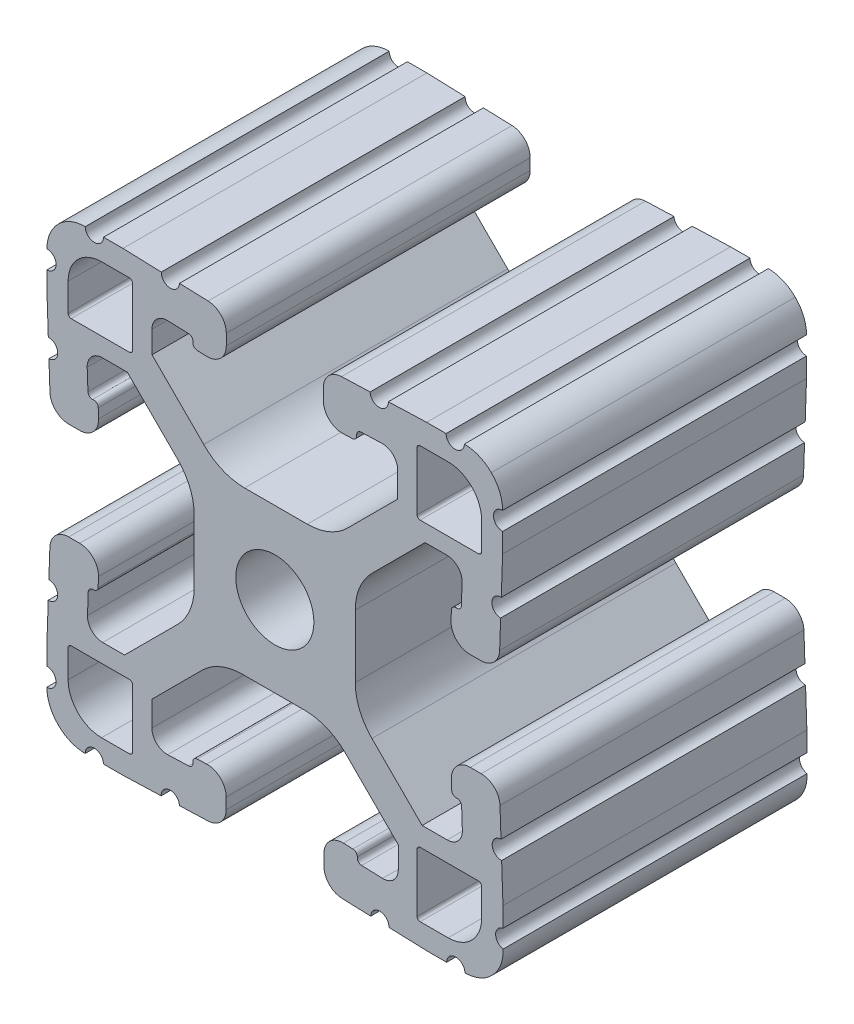
SolidWorks part; units mm, degrees
ref_plane "Front Plane" through (0, 0, 0) normal (0, 0, 1) x (1, 0, 0)
ref_plane "Top Plane" through (0, 0, 0) normal (0, 1, 0) x (1, 0, 0)
ref_plane "Right Plane" through (0, 0, 0) normal (1, 0, 0) x (0, 0, -1)
ref_plane "Plane1" through (0, 0, -25.4) normal (0, 0, -1) x (-1, 0, 0)
sketch "Sketch1" plane through (0, 0, -25.4) normal (0, 0, -1) x (-1, 0, 0)
  line L0 (-83.3577, 88.2941) -> (-83.3577, 93.1709)
  line L1 (-83.1037, 93.4249) -> (-80.767, 93.4249)
  line L2 (-77.9729, 90.6309) -> (-77.9729, 88.2941)
  line L3 (-78.2269, 88.0401) -> (-83.1037, 88.0401)
  line L4 (-83.3577, 59.2291) -> (-83.3577, 64.1059)
  line L5 (-83.1037, 64.3599) -> (-78.2269, 64.3599)
  line L6 (-77.9729, 64.1059) -> (-77.9729, 61.7691)
  line L7 (-80.767, 58.9751) -> (-83.1037, 58.9751)
  line L8 (-107.1423, 93.1709) -> (-107.1423, 88.2941)
  line L9 (-107.3963, 88.0401) -> (-112.2731, 88.0401)
  line L10 (-112.5271, 88.2941) -> (-112.5271, 90.6309)
  line L11 (-109.733, 93.4249) -> (-107.3963, 93.4249)
  line L12 (-107.1423, 64.1059) -> (-107.1423, 59.2291)
  line L13 (-107.3963, 58.9751) -> (-109.733, 58.9751)
  line L14 (-112.5271, 61.7691) -> (-112.5271, 64.1059)
  line L15 (-112.2731, 64.3599) -> (-107.3963, 64.3599)
  line L16 (-88.0437, 91.8626) -> (-86.2967, 91.9236)
  line L17 (-84.9824, 90.6544) -> (-84.9824, 88.8002)
  line L18 (-84.9824, 88.8002) -> (-89.3066, 84.476)
  line L19 (-92.7196, 83.0295) -> (-97.9616, 83.0295)
  line L20 (-101.3202, 84.4207) -> (-105.516, 88.6165)
  line L21 (-105.516, 88.6165) -> (-105.516, 90.7313)
  line L22 (-104.2017, 92.0006) -> (-102.4547, 91.9396)
  line L23 (-101.7262, 91.1059) -> (-100.9297, 91.0781)
  line L24 (-99.2999, 92.6519) -> (-99.2999, 93.5668)
  line L25 (-100.8197, 95.1407) -> (-103.2119, 95.2242)
  line L26 (-104.735, 95.2774) -> (-107.9359, 95.3892)
  line L27 (-107.9359, 95.3892) -> (-109.5615, 95.3892)
  line L28 (-114.2859, 90.6648) -> (-114.2859, 89.0392)
  line L29 (-114.2859, 89.0392) -> (-114.1741, 85.8383)
  line L30 (-114.1209, 84.3152) -> (-114.0374, 81.9231)
  line L31 (-112.4635, 80.4032) -> (-111.5486, 80.4032)
  line L32 (-109.9748, 82.033) -> (-110.0026, 82.8295)
  line L33 (-110.8377, 83.5577) -> (-110.8987, 85.3047)
  line L34 (-109.6294, 86.619) -> (-107.8072, 86.619)
  line L35 (-107.8072, 86.619) -> (-103.3649, 82.1768)
  line L36 (-101.9737, 78.8182) -> (-101.9737, 73.576)
  line L37 (-103.3649, 70.2174) -> (-107.5607, 66.0217)
  line L38 (-107.5607, 66.0217) -> (-109.6524, 66.0217)
  line L39 (-110.9217, 67.336) -> (-110.8607, 69.083)
  line L40 (-110.0322, 69.8124) -> (-110.0043, 70.6089)
  line L41 (-111.5782, 72.2387) -> (-112.4931, 72.2387)
  line L42 (-114.0669, 70.7189) -> (-114.1505, 68.3267)
  line L43 (-114.2036, 66.8036) -> (-114.3154, 63.6027)
  line L44 (-114.3154, 63.6027) -> (-114.3154, 61.9626)
  line L45 (-109.6111, 57.1437) -> (-107.9855, 57.1437)
  line L46 (-107.9855, 57.1437) -> (-104.7846, 57.2555)
  line L47 (-103.2615, 57.3086) -> (-100.8694, 57.3922)
  line L48 (-99.3495, 58.966) -> (-99.3495, 59.8809)
  line L49 (-100.9794, 61.4548) -> (-101.7758, 61.4269)
  line L50 (-102.5054, 60.599) -> (-104.2524, 60.538)
  line L51 (-105.5667, 61.8072) -> (-105.5667, 63.6295)
  line L52 (-105.5667, 63.6295) -> (-101.1311, 68.065)
  line L53 (-97.7725, 69.4562) -> (-92.5304, 69.4562)
  line L54 (-89.1717, 68.065) -> (-84.976, 63.8692)
  line L55 (-84.976, 63.8692) -> (-84.976, 61.7811)
  line L56 (-86.2903, 60.5118) -> (-88.0373, 60.5728)
  line L57 (-88.7596, 61.4332) -> (-89.5561, 61.461)
  line L58 (-91.1859, 59.8872) -> (-91.1859, 58.9723)
  line L59 (-89.6661, 57.3985) -> (-87.2739, 57.3149)
  line L60 (-85.7508, 57.2617) -> (-82.5499, 57.15)
  line L61 (-82.5499, 57.15) -> (-80.9244, 57.15)
  line L62 (-76.2, 61.8744) -> (-76.2, 63.4999)
  line L63 (-76.2, 63.4999) -> (-76.3117, 66.7008)
  line L64 (-76.3649, 68.2239) -> (-76.4484, 70.6161)
  line L65 (-78.0223, 72.1359) -> (-78.9372, 72.1359)
  line L66 (-80.511, 70.5061) -> (-80.4832, 69.7096)
  line L67 (-79.6552, 68.9801) -> (-79.5942, 67.2331)
  line L68 (-80.8634, 65.9188) -> (-82.6857, 65.9188)
  line L69 (-82.6857, 65.9188) -> (-87.1213, 70.3543)
  line L70 (-88.5125, 73.7128) -> (-88.5126, 78.955)
  line L71 (-87.1214, 82.3137) -> (-82.9257, 86.5095)
  line L72 (-82.9257, 86.5095) -> (-80.8375, 86.5095)
  line L73 (-79.5682, 85.1951) -> (-79.6293, 83.4482)
  line L74 (-80.4896, 82.7258) -> (-80.5175, 81.9294)
  line L75 (-78.9436, 80.2995) -> (-78.0287, 80.2995)
  line L76 (-76.4549, 81.8194) -> (-76.3713, 84.2115)
  line L77 (-76.3182, 85.7346) -> (-76.2064, 88.9355)
  line L78 (-76.2064, 88.9355) -> (-76.2064, 90.5611)
  line L79 (-80.9308, 95.2855) -> (-82.5564, 95.2855)
  line L80 (-82.5564, 95.2855) -> (-85.7573, 95.1737)
  line L81 (-87.2803, 95.1205) -> (-89.6725, 95.037)
  line L82 (-91.1924, 93.4632) -> (-91.1924, 92.5483)
  line L83 (-89.5625, 90.9744) -> (-88.7661, 91.0023)
  arc A0 (-83.3577, 93.1709) -> (-83.1037, 93.4249) centre (-83.1037, 93.1709) cw
  arc A1 (-80.767, 93.4249) -> (-77.9729, 90.6309) centre (-80.7669, 90.6309) cw
  arc A2 (-77.9729, 88.2941) -> (-78.2269, 88.0401) centre (-78.2269, 88.2941) cw
  arc A3 (-83.1037, 88.0401) -> (-83.3577, 88.2941) centre (-83.1037, 88.2941) cw
  arc A4 (-83.1037, 58.9751) -> (-83.3577, 59.2291) centre (-83.1037, 59.2291) cw
  arc A5 (-83.3577, 64.1059) -> (-83.1037, 64.3599) centre (-83.1037, 64.1059) cw
  arc A6 (-78.2269, 64.3599) -> (-77.9729, 64.1059) centre (-78.2269, 64.1059) cw
  arc A7 (-77.9729, 61.7691) -> (-80.767, 58.9751) centre (-80.7669, 61.7691) cw
  arc A8 (-107.3963, 93.4249) -> (-107.1423, 93.1709) centre (-107.3963, 93.1709) cw
  arc A9 (-107.1423, 88.2941) -> (-107.3963, 88.0401) centre (-107.3963, 88.2941) cw
  arc A10 (-112.2731, 88.0401) -> (-112.5271, 88.2941) centre (-112.2731, 88.2941) cw
  arc A11 (-112.5271, 90.6309) -> (-109.733, 93.4249) centre (-109.7331, 90.6309) cw
  arc A12 (-107.1423, 59.2291) -> (-107.3963, 58.9751) centre (-107.3963, 59.2291) cw
  arc A13 (-109.733, 58.9751) -> (-112.5271, 61.7691) centre (-109.7331, 61.7691) cw
  arc A14 (-112.5271, 64.1059) -> (-112.2731, 64.3599) centre (-112.2731, 64.1059) cw
  arc A15 (-107.3963, 64.3599) -> (-107.1423, 64.1059) centre (-107.3963, 64.1059) cw
  circle A16 centre (-95.25, 76.2) radius 3.2639
  arc A17 (-88.7661, 91.0023) -> (-88.3984, 91.383) centre (-88.7794, 91.383) ccw
  arc A18 (-88.3984, 91.383) -> (-88.0437, 91.8626) centre (-88.0304, 91.4819) cw
  arc A19 (-86.2967, 91.9236) -> (-84.9824, 90.6544) centre (-86.2524, 90.6544) cw
  arc A20 (-89.3066, 84.476) -> (-92.7196, 83.0295) centre (-92.7196, 87.7793) cw
  arc A21 (-97.9616, 83.0295) -> (-101.3202, 84.4207) centre (-97.9616, 87.7793) cw
  arc A22 (-105.516, 90.7313) -> (-104.2017, 92.0006) centre (-104.246, 90.7313) cw
  arc A23 (-102.4547, 91.9396) -> (-102.087, 91.5588) centre (-102.468, 91.5588) cw
  arc A24 (-102.087, 91.5588) -> (-101.7262, 91.1059) centre (-101.7129, 91.4867) ccw
  arc A25 (-100.9297, 91.0781) -> (-99.2999, 92.6519) centre (-100.8747, 92.6519) ccw
  arc A26 (-99.2999, 93.5668) -> (-100.8197, 95.1407) centre (-100.8747, 93.5668) ccw
  arc A27 (-103.2119, 95.2242) -> (-104.735, 95.2774) centre (-103.9735, 95.2508) cw
  arc A28 (-109.5615, 95.3892) -> (-111.0855, 95.3892) centre (-110.3235, 95.3892) cw
  arc A29 (-111.0855, 95.3892) -> (-113.3432, 94.4465) centre (-111.0855, 92.2142) ccw
  arc A30 (-113.3432, 94.4465) -> (-114.2859, 92.1888) centre (-111.1109, 92.1888) ccw
  arc A31 (-114.2859, 92.1888) -> (-114.2859, 90.6648) centre (-114.2859, 91.4268) cw
  arc A32 (-114.1741, 85.8383) -> (-114.1209, 84.3152) centre (-114.1475, 85.0768) cw
  arc A33 (-114.0374, 81.9231) -> (-112.4635, 80.4032) centre (-112.4635, 81.978) ccw
  arc A34 (-111.5486, 80.4032) -> (-109.9748, 82.033) centre (-111.5486, 81.978) ccw
  arc A35 (-110.0026, 82.8295) -> (-110.3834, 83.1972) centre (-110.3834, 82.8162) ccw
  arc A36 (-110.3834, 83.1972) -> (-110.8377, 83.5577) centre (-110.4569, 83.571) cw
  arc A37 (-110.8987, 85.3047) -> (-109.6294, 86.619) centre (-109.6294, 85.349) cw
  arc A38 (-103.3649, 82.1768) -> (-101.9737, 78.8182) centre (-106.7235, 78.8182) cw
  arc A39 (-101.9737, 73.576) -> (-103.3649, 70.2174) centre (-106.7235, 73.576) cw
  arc A40 (-109.6524, 66.0217) -> (-110.9217, 67.336) centre (-109.6524, 67.2917) cw
  arc A41 (-110.8607, 69.083) -> (-110.4799, 69.4507) centre (-110.4799, 69.0697) cw
  arc A42 (-110.4799, 69.4507) -> (-110.0322, 69.8124) centre (-110.413, 69.8257) ccw
  arc A43 (-110.0043, 70.6089) -> (-111.5782, 72.2387) centre (-111.5782, 70.6639) ccw
  arc A44 (-112.4931, 72.2387) -> (-114.0669, 70.7189) centre (-112.4931, 70.6639) ccw
  arc A45 (-114.1505, 68.3267) -> (-114.2036, 66.8036) centre (-114.1771, 67.5652) cw
  arc A46 (-114.3154, 61.9626) -> (-114.3332, 60.4644) centre (-114.4639, 61.2152) cw
  arc A47 (-114.3332, 60.4644) -> (-113.3928, 58.0864) centre (-111.1605, 60.3441) ccw
  arc A48 (-113.3928, 58.0864) -> (-111.1351, 57.1437) centre (-111.1351, 60.3187) ccw
  arc A49 (-111.1351, 57.1437) -> (-109.6111, 57.1437) centre (-110.3731, 57.1437) cw
  arc A50 (-104.7846, 57.2555) -> (-103.2615, 57.3086) centre (-104.0231, 57.2821) cw
  arc A51 (-100.8694, 57.3922) -> (-99.3495, 58.966) centre (-100.9243, 58.966) ccw
  arc A52 (-99.3495, 59.8809) -> (-100.9794, 61.4548) centre (-100.9243, 59.8809) ccw
  arc A53 (-101.7758, 61.4269) -> (-102.1435, 61.0462) centre (-101.7625, 61.0462) ccw
  arc A54 (-102.1435, 61.0462) -> (-102.5054, 60.599) centre (-102.5187, 60.9797) cw
  arc A55 (-104.2524, 60.538) -> (-105.5667, 61.8072) centre (-104.2967, 61.8072) cw
  arc A56 (-101.1311, 68.065) -> (-97.7725, 69.4562) centre (-97.7725, 64.7064) cw
  arc A57 (-92.5304, 69.4562) -> (-89.1717, 68.065) centre (-92.5304, 64.7064) cw
  arc A58 (-84.976, 61.7811) -> (-86.2903, 60.5118) centre (-86.246, 61.7811) cw
  arc A59 (-88.0373, 60.5728) -> (-88.405, 60.9536) centre (-88.024, 60.9536) cw
  arc A60 (-88.405, 60.9536) -> (-88.7596, 61.4332) centre (-88.7729, 61.0524) ccw
  arc A61 (-89.5561, 61.461) -> (-91.1859, 59.8872) centre (-89.6111, 59.8872) ccw
  arc A62 (-91.1859, 58.9723) -> (-89.6661, 57.3985) centre (-89.6111, 58.9723) ccw
  arc A63 (-87.2739, 57.3149) -> (-85.7508, 57.2617) centre (-86.5124, 57.2883) cw
  arc A64 (-80.9244, 57.15) -> (-79.4004, 57.15) centre (-80.1624, 57.15) cw
  arc A65 (-79.4004, 57.15) -> (-77.1426, 58.0927) centre (-79.4004, 60.325) ccw
  arc A66 (-77.1426, 58.0927) -> (-76.2, 60.3504) centre (-79.375, 60.3504) ccw
  arc A67 (-76.2, 60.3504) -> (-76.2, 61.8744) centre (-76.2, 61.1124) cw
  arc A68 (-76.3117, 66.7008) -> (-76.3649, 68.2239) centre (-76.3383, 67.4624) cw
  arc A69 (-76.4484, 70.6161) -> (-78.0223, 72.1359) centre (-78.0223, 70.5611) ccw
  arc A70 (-78.9372, 72.1359) -> (-80.511, 70.5061) centre (-78.9372, 70.5611) ccw
  arc A71 (-80.4832, 69.7096) -> (-80.1024, 69.342) centre (-80.1024, 69.723) ccw
  arc A72 (-80.1024, 69.342) -> (-79.6552, 68.9801) centre (-80.036, 68.9668) cw
  arc A73 (-79.5942, 67.2331) -> (-80.8634, 65.9188) centre (-80.8634, 67.1888) cw
  arc A74 (-87.1213, 70.3543) -> (-88.5125, 73.7128) centre (-83.7627, 73.7129) cw
  arc A75 (-88.5126, 78.955) -> (-87.1214, 82.3137) centre (-83.7628, 78.9551) cw
  arc A76 (-80.8375, 86.5095) -> (-79.5682, 85.1951) centre (-80.8375, 85.2395) cw
  arc A77 (-79.6293, 83.4482) -> (-80.01, 83.0805) centre (-80.01, 83.4615) cw
  arc A78 (-80.01, 83.0805) -> (-80.4896, 82.7258) centre (-80.1089, 82.7125) ccw
  arc A79 (-80.5175, 81.9294) -> (-78.9436, 80.2995) centre (-78.9436, 81.8743) ccw
  arc A80 (-78.0287, 80.2995) -> (-76.4549, 81.8194) centre (-78.0287, 81.8743) ccw
  arc A81 (-76.3713, 84.2115) -> (-76.3182, 85.7346) centre (-76.3448, 84.9731) cw
  arc A82 (-76.2064, 90.5611) -> (-76.2064, 92.0851) centre (-76.2064, 91.3231) cw
  arc A83 (-76.2064, 92.0851) -> (-77.1491, 94.3428) centre (-79.3814, 92.0851) ccw
  arc A84 (-77.1491, 94.3428) -> (-79.4068, 95.2855) centre (-79.4068, 92.1105) ccw
  arc A85 (-79.4068, 95.2855) -> (-80.9308, 95.2855) centre (-80.1688, 95.2855) cw
  arc A86 (-85.7573, 95.1737) -> (-87.2803, 95.1205) centre (-86.5188, 95.1471) cw
  arc A87 (-89.6725, 95.037) -> (-91.1924, 93.4632) centre (-89.6176, 93.4632) ccw
  arc A88 (-91.1924, 92.5483) -> (-89.5625, 90.9744) centre (-89.6176, 92.5483) ccw
extrude "Boss-Extrude1" add sketch "Sketch1" against normal blind 25.4
